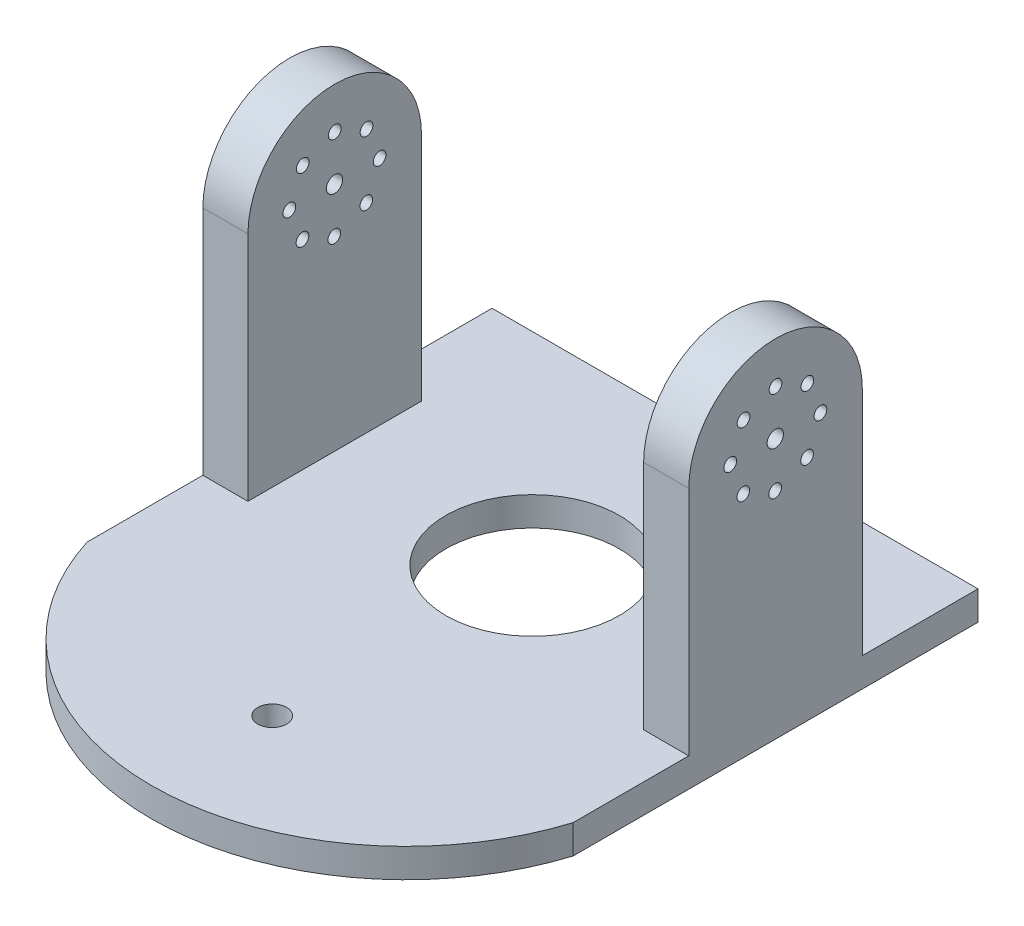
SolidWorks part; units mm, degrees
ref_plane "Front Plane" through (0, 0, 0) normal (0, 0, 1) x (1, 0, 0)
ref_plane "Top Plane" through (0, 0, 0) normal (0, 1, 0) x (1, 0, 0)
ref_plane "Right Plane" through (0, 0, 0) normal (1, 0, 0) x (0, 0, -1)
sketch "Sketch1" plane through (0, 0, 0) normal (0, 1, 0) x (1, 0, 0)
  line L0 (-53.34, 0) -> (53.1768, 0) construction
  line L1 (-53.5032, 44.45) -> (53.1768, 44.45)
  line L2 (-53.5032, 44.45) -> (-53.5032, -44.45)
  line L3 (-0.1632, 0) -> (-0.1632, -111.9811) construction
  line L4 (53.1768, 44.45) -> (53.1768, -44.45)
  line L5 (-53.5032, 44.45) -> (53.1768, -44.45) construction
  line L6 (-53.5032, -44.45) -> (53.1768, 44.45) construction
  line L7 (-0.1632, -57.15) -> (-0.1632, 44.45) construction
  arc A0 (53.1768, -44.45) -> (-53.5032, -44.45) centre (-0.1632, -27.7941) cw
  circle A1 centre (-0.1632, 0) radius 19.05
  circle A6 centre (-0.1632, -57.15) radius 3.175
  dimension "D7" = 6.35
  dimension "D1" = 88.9
  dimension "D2" = 106.68
extrude "Boss-Extrude1" add sketch "Sketch1" along normal blind 6.35
sketch "Sketch6" plane through (0, 6.35, 0) normal (0, 1, 0) x (1, 0, 0)
  line L1 (-53.5032, 19.05) -> (-43.5972, 19.05)
  line L2 (-53.5032, 19.05) -> (-53.5032, -19.05)
  line L3 (-53.5032, -19.05) -> (-43.5972, -19.05)
  line L4 (-43.5972, 19.05) -> (-43.5972, -19.05)
  line L5 (-19.05, 19.05) -> (19.05, 19.05) construction
  line L6 (53.1768, 19.05) -> (43.2708, 19.05)
  line L7 (53.1768, 19.05) -> (53.1768, -19.05)
  line L8 (53.1768, -19.05) -> (43.2708, -19.05)
  line L9 (43.2708, 19.05) -> (43.2708, -19.05)
  line L10 (-19.05, 19.05) -> (-19.05, -19.05) construction
  line L11 (-53.5032, 44.45) -> (-53.5032, -44.45) construction
  line L12 (53.1768, 44.45) -> (53.1768, -44.45) construction
  line L13 (-19.05, -19.05) -> (19.05, -19.05) construction
  line L14 (-53.34, 0) -> (53.1768, 0) construction
  line L15 (19.05, 19.05) -> (19.05, -19.05) construction
  line L16 (-19.05, 19.05) -> (19.05, -19.05) construction
  line L17 (-19.05, -19.05) -> (19.05, 19.05) construction
  point P12 (0, 0)
  point P24 (0, 0)
  point P27 (0, 0)
  point P30 (0, 0)
  point P33 (0, 0)
  dimension "D1" = 38.1
  dimension "D2" = 86.868
  dimension "D3" = 19.05
  dimension "D4" = 9.906
  dimension "D6" = 38.1
  dimension "D7" = 38.1
  dimension "D9" = 4
extrude "Boss-Extrude2" add sketch "Sketch6" along normal blind 76.2
sketch "Sketch7" plane through (-53.5032, 0, 0) normal (-1, 0, 0) x (0, 0, 1)
  line L0 (0, 82.55) -> (0, 0) construction
  line L1 (-19.05, 82.55) -> (19.05, 82.55) construction
  line L2 (-44.45, 0) -> (44.45, 0) construction
  line L3 (-19.05, 44.45) -> (19.05, 44.45) construction
  line L4 (-19.05, 82.55) -> (-19.05, 6.35) construction
  line L5 (19.05, 82.55) -> (19.05, 6.35) construction
  line L6 (-19.05, 57.1052) -> (-19.05, 82.55)
  line L7 (-19.0052, 13.0101) -> (19.0948, 13.0101) construction
  line L8 (-19.0052, 32.0601) -> (19.0948, 32.0601) construction
  line L9 (-19.05, 82.55) -> (19.05, 82.55)
  line L10 (19.05, 82.55) -> (19.05, 57.1948)
  circle A0 centre (-6.9915, 64.1229) radius 1.397
  circle A1 centre (0, 67.056) radius 1.397
  circle A2 centre (7.0177, 64.1863) radius 1.397
  circle A3 centre (0.0448, 57.15) radius 12.7 construction
  circle A4 centre (9.9508, 57.1948) radius 1.397
  circle A5 centre (7.0811, 50.1771) radius 1.397
  circle A6 centre (0.0896, 47.244) radius 1.397
  circle A7 centre (-6.9281, 50.1137) radius 1.397
  arc A8 (-19.05, 57.1052) -> (19.05, 57.1948) centre (0.0001, 57.1052) cw
  circle A11 centre (-9.8612, 57.1052) radius 1.397
  circle A12 centre (0.0448, 57.15) radius 1.7859
  point P28 (0.0448, 57.15)
  point P52 (-9.8612, 57.1052)
  point P77 (0.0448, 57.15)
  dimension "D4" = 9.906
  dimension "D6" = 57.15
extrude "Cut-Extrude1" cut sketch "Sketch7" against normal through all
